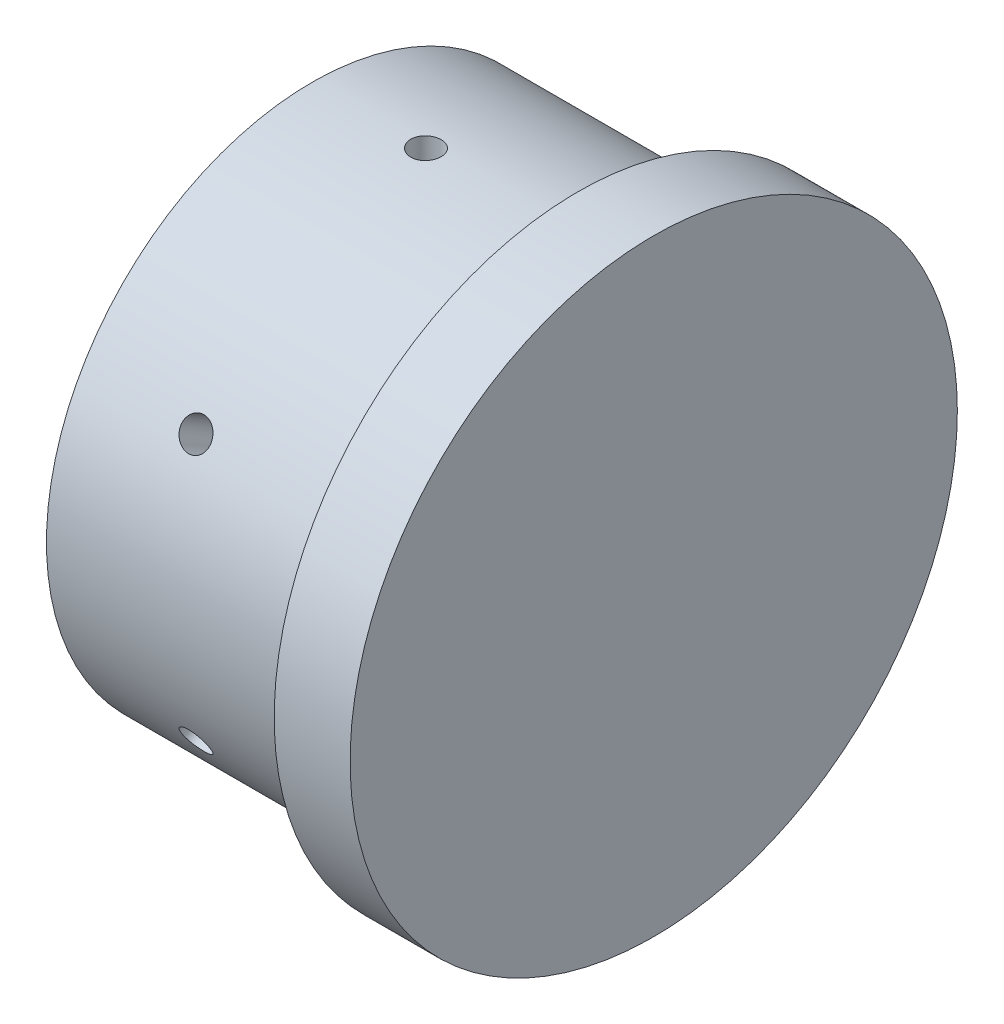
SolidWorks part; units mm, degrees
ref_plane "Front Plane" through (0, 0, 0) normal (0, 0, 1) x (1, 0, 0)
ref_plane "Top Plane" through (0, 0, 0) normal (0, 1, 0) x (1, 0, 0)
ref_plane "Right Plane" through (0, 0, 0) normal (1, 0, 0) x (0, 0, -1)
sketch "Sketch1" plane through (0, 0, 0) normal (1, 0, 0) x (0, 0, -1)
  circle A0 centre (0, 0) radius 35
  dimension "D1" = 70
extrude "Boss-Extrude1" add sketch "Sketch1" along normal blind 35
sketch "Sketch2" plane through (35, 0, 0) normal (1, 0, 0) x (0, 0, -1)
  circle A0 centre (0, 0) radius 40
  dimension "D1" = 80
extrude "Boss-Extrude2" add sketch "Sketch2" along normal blind 10
ref_plane "Bolts" through (0, 35, 0) normal (0, 1, 0) x (1, 0, 0)
sketch "Sketch3" plane through (0, 35, 0) normal (0, 1, 0) x (1, 0, 0)
  line L0 (35, 0) -> (15, 0) construction
  line L1 (35, 40) -> (35, -40) construction
  circle A0 centre (15, 0) radius 2
  dimension "D2" = 4
  dimension "D1" = 20
extrude "Cut-Extrude1" cut sketch "Sketch3" against normal blind 10
pattern_circular "CirPattern1" count 6 over 360 about axis through (0, 0, 0) along (1, 0, 0) of "Cut-Extrude1"
